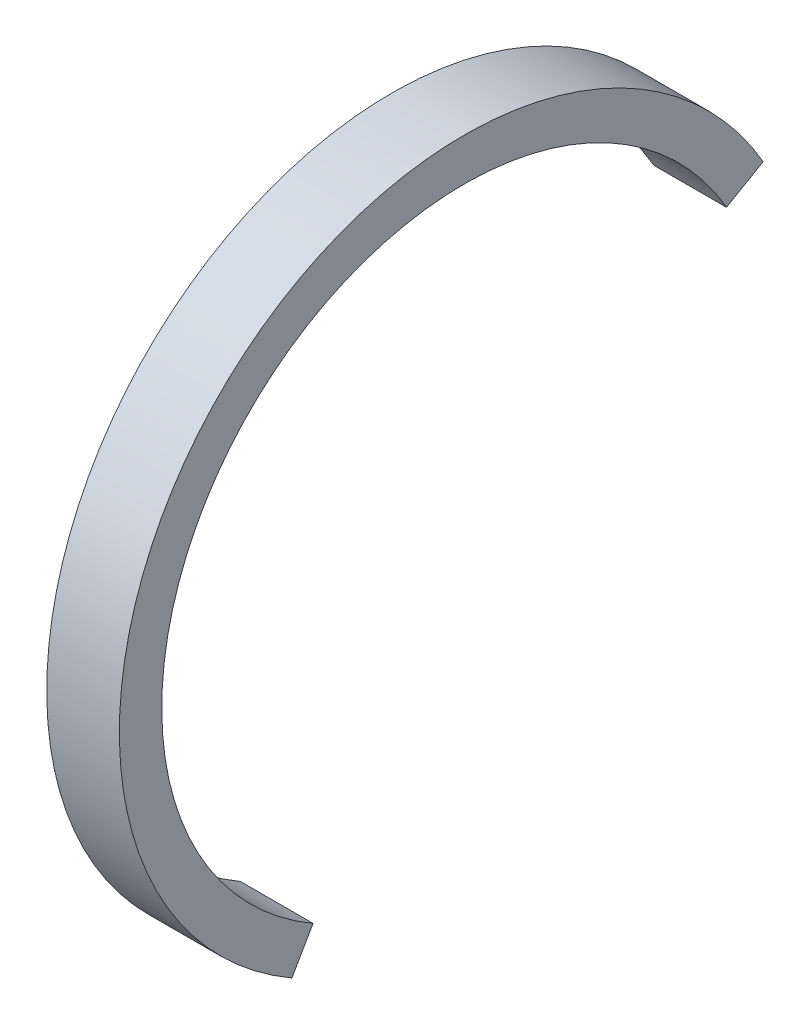
SolidWorks part; units mm, degrees
ref_plane "Front Plane" through (0, 0, 0) normal (0, 0, 1) x (1, 0, 0)
ref_plane "Top Plane" through (0, 0, 0) normal (0, 1, 0) x (1, 0, 0)
ref_plane "Right Plane" through (0, 0, 0) normal (1, 0, 0) x (0, 0, -1)
sketch "Sketch1" plane through (0, 0, 0) normal (1, 0, 0) x (0, 0, -1)
  line L0 (-34.8113, 0) -> (-25, 0) construction
  line L3 (-12.5, -21.6506) -> (-14.25, -24.6817)
  line L4 (21.6506, 12.5) -> (24.6817, 14.25)
  line L5 (0, 0) -> (37.5063, 0) construction
  arc A0 (24.6817, 14.25) -> (-14.25, -24.6817) centre (0, 0) ccw
  arc A2 (21.6506, 12.5) -> (-12.5, -21.6506) centre (0, 0) ccw
  dimension "D1" = 57
  dimension "D5" = 50
extrude "Boss-Extrude1" add sketch "Sketch1" along normal blind 6
